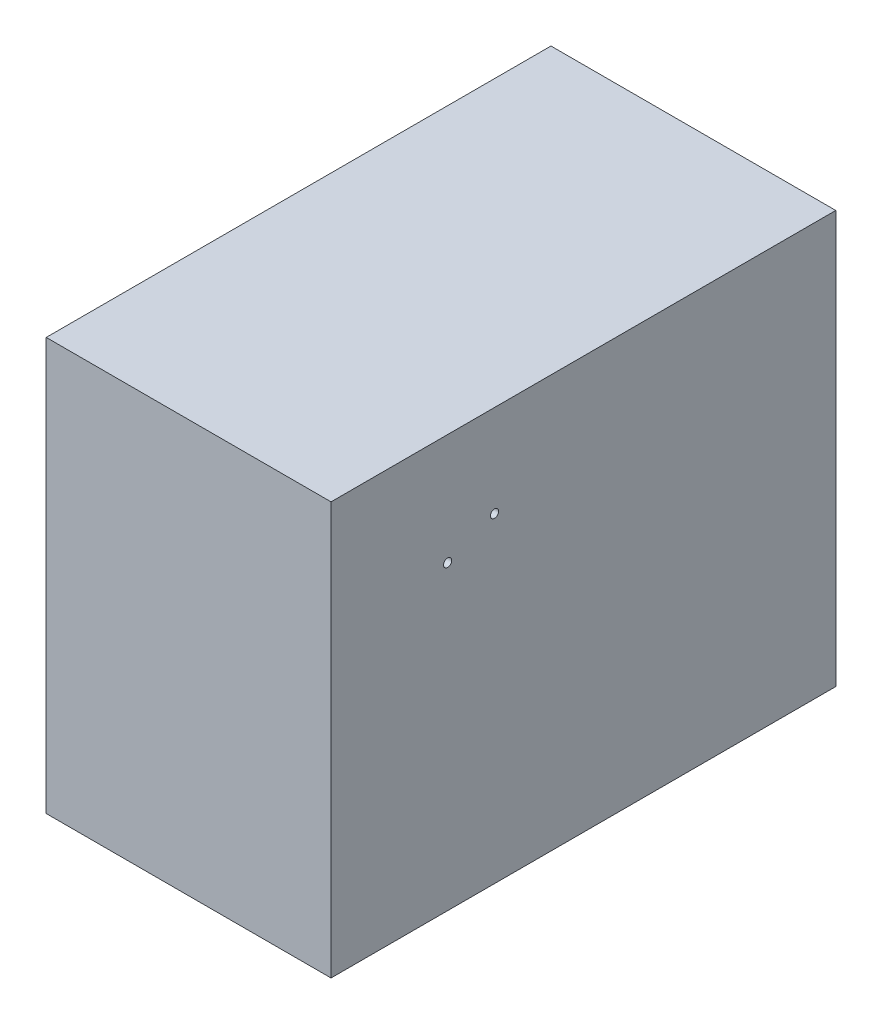
SolidWorks part; units mm, degrees
ref_plane "Front Plane" through (0, 0, 0) normal (0, 0, 1) x (1, 0, 0)
ref_plane "Top Plane" through (0, 0, 0) normal (0, 1, 0) x (1, 0, 0)
ref_plane "Right Plane" through (0, 0, 0) normal (1, 0, 0) x (0, 0, -1)
sketch "Sketch1" plane through (0, 0, 0) normal (0, 0, 1) x (1, 0, 0)
  line L1 (-50.165, -72.6313) -> (50.165, -72.6313)
  line L2 (-50.165, -72.6313) -> (-50.165, 72.6313)
  line L3 (-50.165, 72.6313) -> (50.165, 72.6313)
  line L4 (50.165, -72.6313) -> (50.165, 72.6313)
  line L5 (-50.165, -72.6313) -> (50.165, 72.6313) construction
  line L6 (-50.165, 72.6313) -> (50.165, -72.6313) construction
  point P0 (0, 0)
  dimension "D1" = 100.33
  dimension "D2" = 145.2626
extrude "Boss-Extrude1" add sketch "Sketch1" along normal blind 177.8
sketch "Sketch2" plane through (50.165, 0, 0) normal (1, 0, 0) x (0, 0, -1)
  line L0 (-136.7282, 33.5407) -> (-120.2182, 40.2463) construction
  line L1 (-177.8, -72.6313) -> (-177.8, 72.6313) construction
  line L2 (-138.176, 32.0929) -> (-118.7704, 32.0929) construction
  line L3 (-138.176, 32.0929) -> (-138.176, 41.6941) construction
  line L4 (-138.176, 41.6941) -> (-118.7704, 41.6941) construction
  line L5 (-118.7704, 32.0929) -> (-118.7704, 41.6941) construction
  line L6 (-138.176, 32.0929) -> (-118.7704, 41.6941) construction
  line L7 (-138.176, 41.6941) -> (-118.7704, 32.0929) construction
  line L8 (-177.8, -72.6313) -> (0, -72.6313) construction
  circle A0 centre (-136.7282, 33.5407) radius 1.4478
  circle A1 centre (-120.2182, 40.2463) radius 1.4478
  point P4 (-128.4732, 36.8935)
  dimension "D2" = 2.8956
  dimension "D1" = 16.51
  dimension "D3" = 6.7056
  dimension "D4" = 39.624
  dimension "D5" = 104.7242
extrude "Cut-Extrude1" cut sketch "Sketch2" against normal blind 177.8
